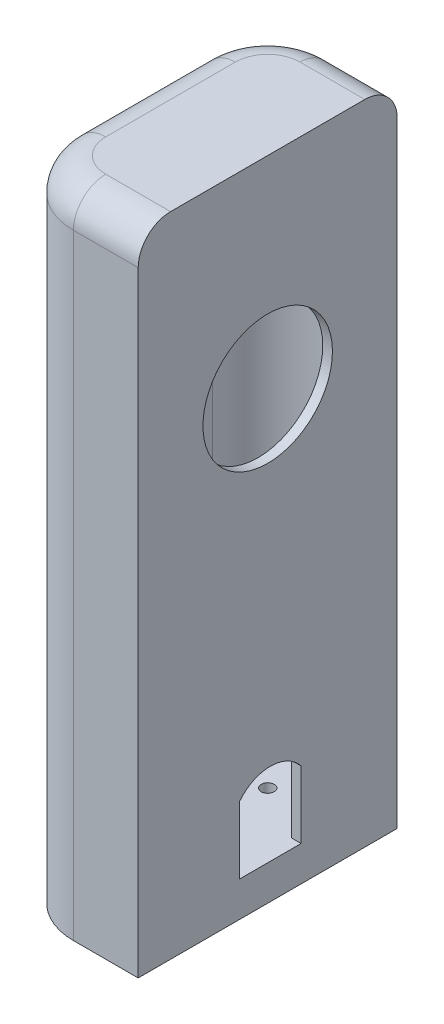
SolidWorks part; units mm, degrees
other "Markup1"
sketch "Sketch12" plane through (5.9548, 0, 20.4092) normal (0.9902, -0.127, 0.0585) x (0.1293, 0.9909, -0.0372)
ref_plane "Front Plane" through (0, 0, 0) normal (0, 0, 1) x (1, 0, 0)
ref_plane "Top Plane" through (0, 0, 0) normal (0, 1, 0) x (1, 0, 0)
ref_plane "Right Plane" through (0, 0, 0) normal (1, 0, 0) x (0, 0, -1)
sketch "Sketch1" plane through (0, 0, 0) normal (0, 1, 0) x (1, 0, 0)
  line L0 (5.9548, -0.4092) -> (5.9548, -20.4092)
  line L1 (-14.0452, 9.5908) -> (-14.0452, -10.4092)
  line L2 (5.9548, 19.5908) -> (5.9548, -0.4092)
  line L3 (-14.0452, 9.5908) -> (-14.0452, -0.4092)
  line L4 (-4.0452, 19.5908) -> (5.9548, 19.5908)
  line L5 (-4.0452, -20.4092) -> (5.9548, -20.4092)
  arc A0 (-14.0452, -10.4092) -> (-4.0452, -20.4092) centre (-4.0452, -10.4092) ccw
  arc A1 (-4.0452, 19.5908) -> (-14.0452, 9.5908) centre (-4.0452, 9.5908) ccw
  point P2 (15.9548, -0.4092)
extrude "Boss-Extrude1" add sketch "Sketch1" along normal blind 100 contours L4 A1 L1 A0 L5 L0 L2
sketch "Sketch2" plane through (5.9548, 0, 0) normal (1, 0, 0) x (0, 0, -1)
  line L0 (-0.4092, 100) -> (-0.4092, 68.83) construction
  line L1 (19.5908, 100) -> (-20.4092, 100) construction
  circle A0 centre (-0.4092, 68.83) radius 10
  circle A1 centre (0, 15.9556) radius 3.9686
  dimension "D2" = 20
  dimension "D1" = 31.17
extrude "Cut-Extrude1" cut sketch "Sketch2" against normal blind 7.5 contours A0
sketch "Sketch4" plane through (0, 0, 0) normal (0, 0, 1) x (1, 0, 0)
  line L0 (-1.5452, 58.83) -> (-1.5452, 78.83) construction
  line L1 (-1.5452, 89.7776) -> (3.4548, 89.7776)
  line L2 (-1.5452, 89.7776) -> (-1.5452, 12.7776)
  line L4 (3.4548, 89.7776) -> (3.4548, 12.7776)
  line L5 (0.9548, 51.2776) -> (0.9548, 89.7776) construction
  line L6 (-1.5452, 51.2776) -> (3.4548, 51.2776) construction
  line L7 (-1.5452, 12.7776) -> (-15.4529, 12.7776)
  line L9 (3.4548, 12.7776) -> (3.4548, 5.4097)
  line L10 (3.4548, 5.4097) -> (-15.4529, 5.4097)
  line L11 (-15.4529, 12.7776) -> (-15.4529, 5.4097)
  point P872 (-5.9991, 9.0936)
  point P1176 (0.9548, 51.2776)
  dimension "D1" = 5
  dimension "D2" = 77
extrude "Cut-Extrude2" cut sketch "Sketch4" against normal mid plane 9.5
sketch "Sketch6" plane through (0, 0, 0) normal (0, -1, 0) x (1, 0, 0)
  arc A0 (-4.0452, 20.4092) -> (-14.0452, 10.4092) centre (-4.0452, 10.4092) ccw construction
  arc A1 (-4.0452, 20.4092) -> (-14.0452, 10.4092) centre (-4.0452, 10.4092) ccw
  arc A2 (-14.0452, -9.5908) -> (-4.0452, -19.5908) centre (-4.0452, -9.5908) ccw construction
  arc A3 (-14.0452, -9.5908) -> (-4.0452, -19.5908) centre (-4.0452, -9.5908) ccw
  circle A4 centre (-4.0452, 10.4092) radius 1
  circle A5 centre (-4.0452, -9.5908) radius 1
  dimension "D1" = 2
  dimension "D2" = 2
extrude "Cut-Extrude3" cut sketch "Sketch6" against normal blind 6 contours A5 | A4
sketch "Sketch7" plane through (3.4548, 0, 0) normal (-1, 0, 0) x (0, 0, 1)
  line L0 (-4.75, 5.4097) -> (4.75, 5.4097) construction
  line L1 (-4.75, 5.4097) -> (-4.75, 12.7776) construction
  line L2 (4.75, 5.4097) -> (4.75, 59.8213) construction
  line L3 (-4.75, 12.7776) -> (4.75, 12.7776) construction
  line L4 (-4.75, 5.4097) -> (4.75, 5.4097)
  line L5 (-4.75, 5.4097) -> (-4.75, 12.7776)
  line L6 (4.75, 5.4097) -> (4.75, 59.8213)
  line L7 (-4.75, 12.7776) -> (4.75, 12.7776)
  line M1 (-4.75, 60.2636) -> (-4.75, 5.4097)
  line M2 (-4.75, 5.4097) -> (4.75, 5.4097)
  line M3 (4.75, 5.4097) -> (4.75, 59.8213)
extrude "Cut-Extrude4" cut sketch "Sketch7" against normal blind 6 contours L7 M1 M2 M3
sketch "Sketch8" plane through (-14.0452, 0, 0) normal (-1, 0, 0) x (0, 0, 1)
  line L0 (4.75, 5.4097) -> (-4.75, 5.4097) construction
  line L1 (-4.75, 5.4097) -> (-4.75, 12.7776) construction
  line L2 (4.75, 5.4097) -> (4.75, 12.7776) construction
  line L3 (-4.75, 12.7776) -> (4.75, 12.7776) construction
  line L4 (4.75, 5.4097) -> (-4.75, 5.4097)
  line L5 (-4.75, 5.4097) -> (-4.75, 12.7776)
  line L6 (4.75, 5.4097) -> (4.75, 12.7776)
  line L7 (-4.75, 12.7776) -> (4.75, 12.7776)
extrude "Boss-Extrude2" add sketch "Sketch8" against normal up to surface (12.5 mm away) up to face at (-1.5452, 60.0538, 0.1023)
sketch "Sketch10" plane through (5.9548, 0, 0) normal (1, 0, 0) x (0, 0, -1)
  circle A0 centre (-0.4092, 68.83) radius 10 construction
  circle A1 centre (-0.4092, 68.83) radius 10
extrude "Cut-Extrude5" cut sketch "Sketch10" against normal blind 68
fillet "Fillet1" radius 5 5 edges at (-11.1163, 100, -16.6619) (-14.0452, 100, 0.4092) (-11.1163, 100, 17.4803) (0.9548, 100, 20.4092) (0.9548, 100, -19.5908)
sketch "Sketch11" plane through (-1.5452, 0, 0) normal (1, 0, 0) x (0, 0, -1)
  line L3 (-4.75, 59.8213) -> (-4.75, 5.4097)
  line L4 (-4.75, 5.4097) -> (4.75, 5.4097)
  line L5 (4.75, 5.4097) -> (4.75, 60.2636)
  line L6 (-4.75, 59.8213) -> (-4.75, 5.4097)
  line L7 (-4.75, 5.4097) -> (4.75, 5.4097)
  line L8 (4.75, 5.4097) -> (4.75, 60.2636)
  arc A1 (-4.75, 59.8213) -> (4.75, 60.2636) centre (-0.4092, 68.83) ccw
  arc A2 (-4.75, 59.8213) -> (4.75, 60.2636) centre (-0.4092, 68.83) ccw
  dimension "D1" = 0
extrude "Cut-Extrude6" cut sketch "Sketch11" against normal blind 5
sketch "Sketch13" plane through (5.9548, 0, 0) normal (1, 0, 0) x (0, 0, -1)
  line L0 (-4.75, 12.7776) -> (4.75, 12.7776)
  line L1 (-4.75, 12.7776) -> (-4.75, 15.7776)
  line L2 (4.75, 12.7776) -> (4.75, 15.7776)
  line L3 (-4.75, 15.7776) -> (4.75, 15.7776)
  dimension "D1" = 3
extrude "Cut-Extrude7" cut sketch "Sketch13" against normal blind 5
sketch "Sketch14" plane through (5.9548, 0, 0) normal (1, 0, 0) x (0, 0, -1)
  line L0 (4.75, 15.7776) -> (-4.75, 15.7776) construction
  line L1 (4.75, 15.7776) -> (-4.75, 15.7776)
  arc A0 (-4.75, 15.7776) -> (4.75, 15.7776) centre (0, 12.1162) cw
extrude "Cut-Extrude8" cut sketch "Sketch14" against normal up to surface (12.5 mm away) up to face at (-6.5452, 32.4257, -0.014)
sketch "Sketch16" plane through (-1.5452, 0, 0) normal (1, 0, 0) x (0, 0, -1)
  line L3 (4.75, 77.3964) -> (4.75, 89.7776)
  line L4 (4.75, 89.7776) -> (-4.75, 89.7776)
  line L5 (-4.75, 89.7776) -> (-4.75, 77.8387)
  line L6 (4.75, 77.3964) -> (4.75, 89.7776)
  line L7 (4.75, 89.7776) -> (-4.75, 89.7776)
  line L8 (-4.75, 89.7776) -> (-4.75, 77.8387)
  arc A0 (-4.75, 89.7776) -> (4.75, 89.7776) centre (0, 87.9744) cw
  arc A1 (4.75, 77.3964) -> (-4.75, 77.8387) centre (-0.4092, 68.83) ccw
  arc A2 (4.75, 77.3964) -> (-4.75, 77.8387) centre (-0.4092, 68.83) ccw
  line M7 (4.75, 89.7776) -> (-4.75, 89.7776)
  dimension "D1" = 0
extrude "Cut-Extrude9" cut sketch "Sketch16" along normal up to vertex (5 mm away) contours A0 M7
sketch "Sketch17" plane through (0, 5.4097, 0) normal (0, 1, 0) x (1, 0, 0)
  line L0 (4.4548, 18.0908) -> (-4.0452, 18.0908)
  line L1 (-12.5452, 9.5908) -> (-12.5452, -10.4092)
  line L2 (-4.0452, -18.9092) -> (4.4548, -18.9092)
  line L3 (4.4548, -18.9092) -> (4.4548, 18.0908)
  line L4 (5.9548, 19.5908) -> (-4.0452, 19.5908)
  line L5 (5.9548, -20.4092) -> (5.9548, 19.5908)
  line L6 (-4.0452, -20.4092) -> (5.9548, -20.4092)
  line L7 (-14.0452, 9.5908) -> (-14.0452, -10.4092)
  line L8 (5.9548, 19.5908) -> (-4.0452, 19.5908)
  line L9 (5.9548, -20.4092) -> (5.9548, 19.5908)
  line L10 (-4.0452, -20.4092) -> (5.9548, -20.4092)
  line L11 (-14.0452, 9.5908) -> (-14.0452, -10.4092)
  arc A0 (-4.0452, 18.0908) -> (-12.5452, 9.5908) centre (-4.0452, 9.5908) ccw
  arc A1 (-12.5452, -10.4092) -> (-4.0452, -18.9092) centre (-4.0452, -10.4092) ccw
  arc A2 (-14.0452, -10.4092) -> (-4.0452, -20.4092) centre (-4.0452, -10.4092) ccw
  arc A3 (-4.0452, 19.5908) -> (-14.0452, 9.5908) centre (-4.0452, 9.5908) ccw
  arc A4 (-14.0452, -10.4092) -> (-4.0452, -20.4092) centre (-4.0452, -10.4092) ccw
  arc A6 (-4.0452, 19.5908) -> (-14.0452, 9.5908) centre (-4.0452, 9.5908) ccw construction
  line M7 (5.9548, 4.75) -> (-6.5452, 4.75)
  line M8 (-6.5452, 4.75) -> (-6.5452, -4.75)
  line M9 (-6.5452, -4.75) -> (5.9548, -4.75)
  dimension "D1" = 0
  dimension "D2" = 1.5
extrude "Cut-Extrude11" cut sketch "Sketch17" along normal blind 90 contours L1 A1 L2 L3 L0 A0 M9 M8 M7 | L3 M9 M7 M8
